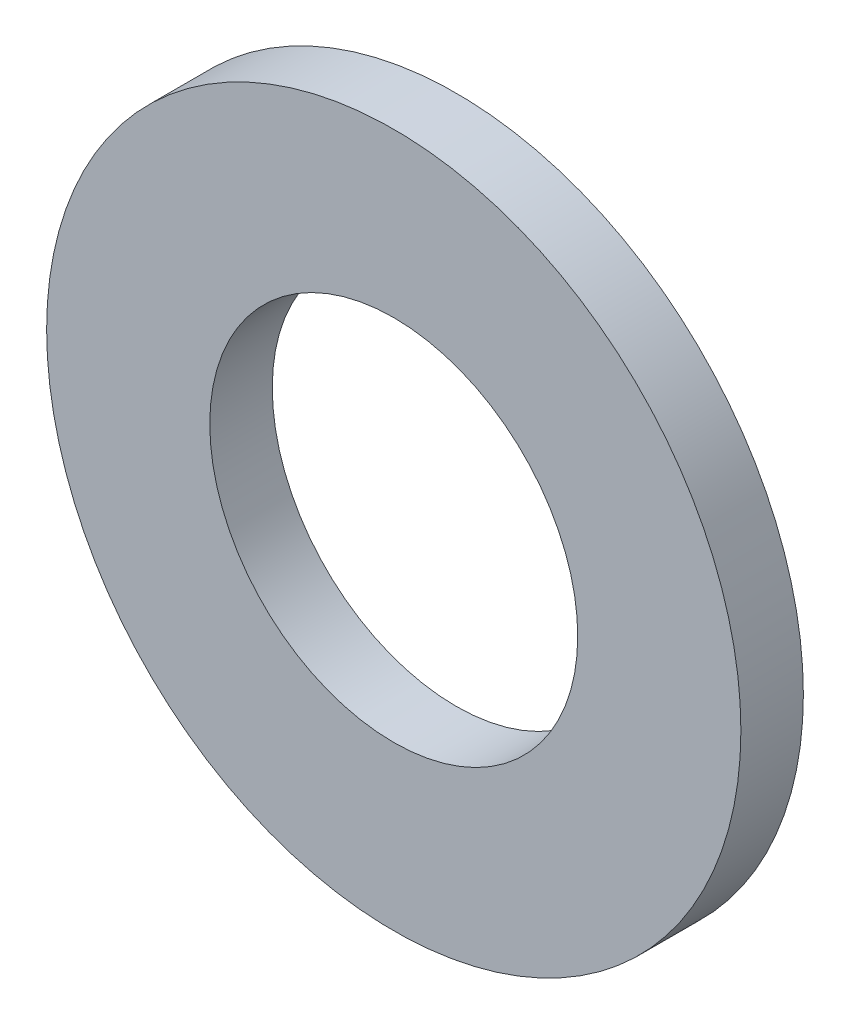
SolidWorks part; units mm, degrees
material "AISI 304"
ref_plane "Front Plane" through (0, 0, 0) normal (0, 0, 1) x (1, 0, 0)
ref_plane "Top Plane" through (0, 0, 0) normal (0, 1, 0) x (1, 0, 0)
ref_plane "Right Plane" through (0, 0, 0) normal (1, 0, 0) x (0, 0, -1)
sketch "Sketch1" plane through (0, 0, 0) normal (0, 0, 1) x (1, 0, 0)
  circle A0 centre (0, 0) radius 2.65
  circle A1 centre (0, 0) radius 5
  dimension "ID" = 5.3
  dimension "OD" = 10
extrude "Extrude1" add sketch "Sketch1" against normal blind 0.9
